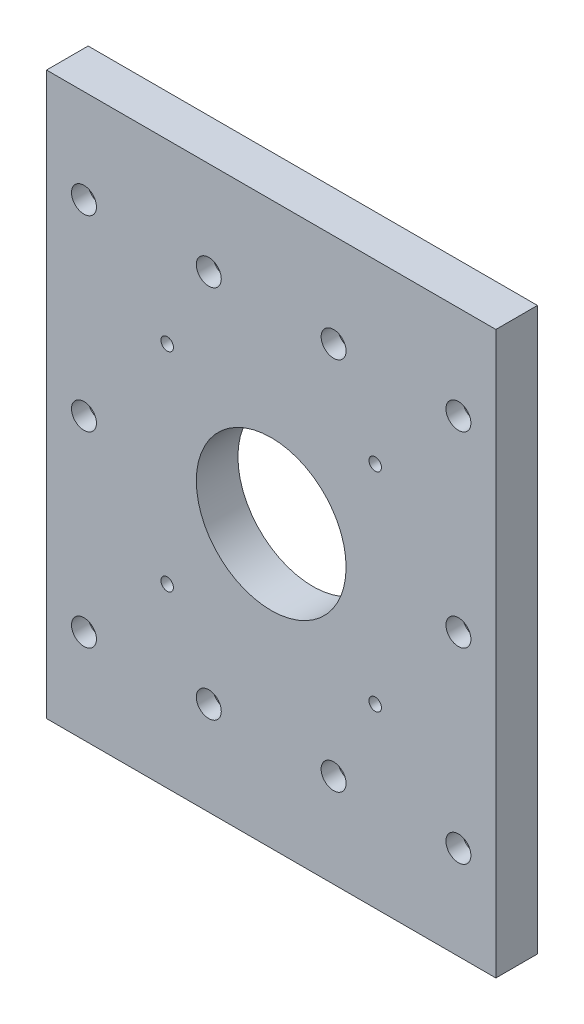
SolidWorks part; units mm, degrees
material "7079 Alloy"
ref_plane "Front" through (0, 0, 0) normal (0, 0, 1) x (1, 0, 0)
ref_plane "Top" through (0, 0, 0) normal (0, 1, 0) x (1, 0, 0)
ref_plane "Right" through (0, 0, 0) normal (1, 0, 0) x (0, 0, -1)
sketch "Sketch1" plane through (0, 0, 0) normal (0, 0, 1) x (1, 0, 0)
  line L0 (0, 135) -> (5, 135)
  line L1 (0, 0) -> (40, 0)
  line L2 (40, 135) -> (64, 135)
  line L3 (0, 135) -> (40, 135)
  line L4 (64, 135) -> (74, 135)
  line L5 (64, 0) -> (40, 0)
  line L6 (0, 135) -> (-24, 135)
  line L8 (-24, 0) -> (0, 0)
  line L9 (74, 135) -> (74, 0)
  line L10 (74, 0) -> (64, 0)
  line L11 (-24, 135) -> (-34, 135)
  line L12 (-34, 135) -> (-34, 0)
  line L13 (-34, 0) -> (-24, 0)
  circle A0 centre (5, 112.5) radius 3
  circle A1 centre (45, 92.5) radius 1.5
  circle A2 centre (45, 42.5) radius 1.5
  circle A3 centre (35, 112.5) radius 3
  circle A4 centre (5, 22.5) radius 3
  circle A5 centre (-5, 42.5) radius 1.5
  circle A6 centre (-5, 92.5) radius 1.5
  circle A7 centre (35, 22.5) radius 3
  circle A8 centre (-25, 112.5) radius 3
  circle A9 centre (65, 112.5) radius 3
  circle A10 centre (65, 22.5) radius 3
  circle A11 centre (-25, 22.5) radius 3
  circle A12 centre (65, 67.5) radius 3
  circle A13 centre (-25, 67.5) radius 3
  dimension "D3" = 30
  dimension "D4" = 30
  dimension "D5" = 22.5
  dimension "D1" = 135
  dimension "D2" = 40
extrude "Extrude1" add sketch "Sketch1" along normal blind 10
sketch "Sketch2" plane through (0, 0, 0) normal (0, 0, -1) x (-1, 0, 0)
  circle A0 centre (-35, 112.5) radius 5
  circle A1 centre (-65, 112.5) radius 5
  circle A2 centre (-65, 22.5) radius 5
  circle A3 centre (-5, 112.5) radius 5
  circle A4 centre (-35, 22.5) radius 5
  circle A5 centre (25, 22.5) radius 5
  circle A6 centre (25, 112.5) radius 5
  circle A7 centre (-5, 22.5) radius 5
  circle A8 centre (-65, 67.5) radius 5
  circle A9 centre (25, 67.5) radius 5
extrude "Cut-Extrude1" cut sketch "Sketch2" against normal blind 6
sketch "Sketch5" plane through (0, 0, 0) normal (0, 0, -1) x (-1, 0, 0)
  circle A0 centre (5, 92.5) radius 1.5
  circle A1 centre (-45, 92.5) radius 1.5
  circle A2 centre (-45, 42.5) radius 1.5
  circle A3 centre (5, 42.5) radius 1.5
extrude "Cut-Extrude4" cut sketch "Sketch5" against normal blind 10
sketch "Sketch3" plane through (0, 0, 0) normal (0, 0, -1) x (-1, 0, 0)
  circle A0 centre (-20, 67.5) radius 18
extrude "Cut-Extrude2" cut sketch "Sketch3" against normal blind 20
